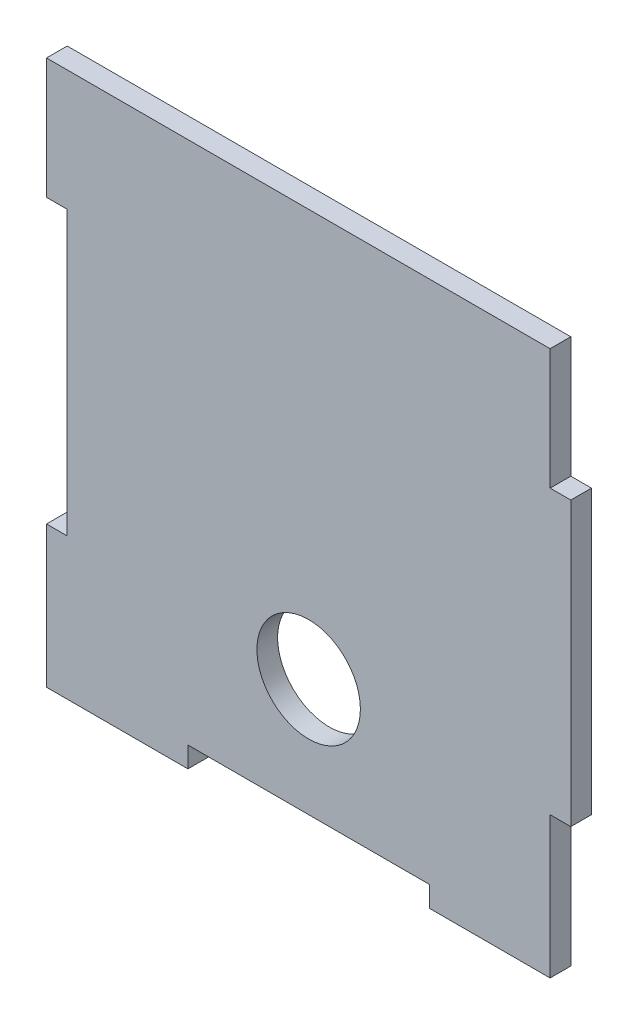
SolidWorks part; units mm, degrees
ref_plane "Front Plane" through (0, 0, 0) normal (0, 0, 1) x (1, 0, 0)
ref_plane "Top Plane" through (0, 0, 0) normal (0, 1, 0) x (1, 0, 0)
ref_plane "Right Plane" through (0, 0, 0) normal (1, 0, 0) x (0, 0, -1)
sketch "Sketch1" plane through (0, 0, 0) normal (0, 0, 1) x (1, 0, 0)
  line L0 (0, 35) -> (0, -38) construction
  line L5 (-35, 38) -> (-17.5, 38)
  line L6 (-35, 20.5) -> (-35, -20.5)
  line L7 (-17.5, -38) -> (17.5, -38)
  line L24 (35, 38) -> (35, 20.5)
  line L25 (-35, 38) -> (35, -38) construction
  line L26 (-35, -38) -> (35, 38) construction
  line L27 (-35, 0) -> (35, 0) construction
  line L31 (-35, -20.5) -> (-38, -20.5)
  line L32 (-35, 20.5) -> (-38, 20.5)
  line L33 (-38, 20.5) -> (-38, 38)
  line L34 (-38, 38) -> (-35, 38)
  line L35 (-38, -20.5) -> (-38, -38)
  line L36 (-17.5, 38) -> (17.5, 38)
  line L37 (35, -38) -> (35, -41)
  line L38 (35, -20.5) -> (38, -20.5)
  line L39 (35, -41) -> (17.5, -41)
  line L40 (35, 20.5) -> (38, 20.5)
  line L41 (17.5, -41) -> (17.5, -38)
  line L42 (-17.5, -38) -> (-17.5, -41)
  line L43 (38, 20.5) -> (38, -20.5)
  line L45 (-35, -41) -> (-17.5, -41)
  line L46 (17.5, 38) -> (35, 38)
  line L47 (35, -20.5) -> (35, -38)
  line L48 (-38, -38) -> (-38, -41)
  line L49 (-38, -41) -> (-35, -41)
  point P0 (0, 0)
  dimension "D1" = 76
  dimension "D2" = 70
  dimension "D3" = 17.5
  dimension "D4" = 17.5
  dimension "D5" = 3
  dimension "D6" = 3
  dimension "D7" = 3
extrude "Boss-Extrude1" add sketch "Sketch1" along normal blind 3
sketch "Sketch2" plane through (0, 0, 3) normal (0, 0, 1) x (1, 0, 0)
  line L5 (-38, -41) -> (-17.5, -41) construction
  circle A0 centre (0, -21) radius 7.5
  point P4 (0, 0)
  dimension "D1" = 15
  dimension "D2" = 20
extrude "Cut-Extrude1" cut sketch "Sketch2" against normal blind 3
